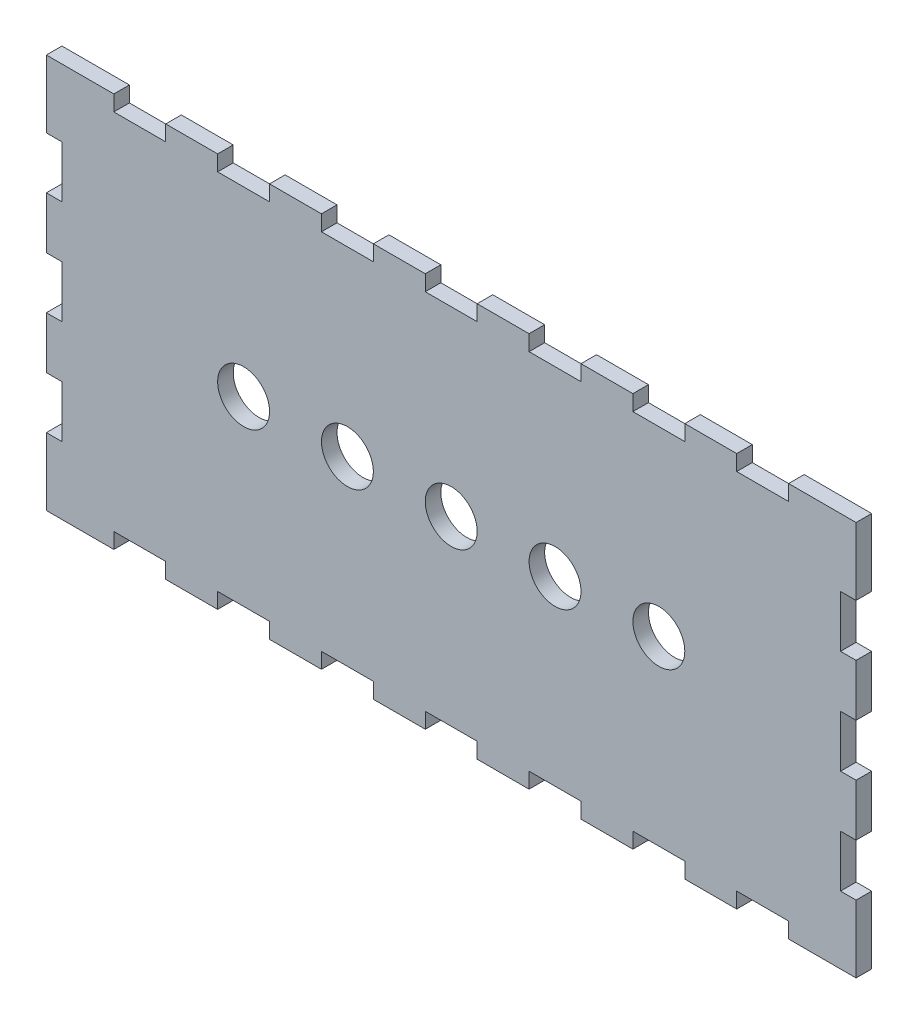
SolidWorks part; units mm, degrees
ref_plane "Front Plane" through (0, 0, 0) normal (0, 0, 1) x (1, 0, 0)
ref_plane "Top Plane" through (0, 0, 0) normal (0, 1, 0) x (1, 0, 0)
ref_plane "Right Plane" through (0, 0, 0) normal (1, 0, 0) x (0, 0, -1)
sketch "Sketch1" plane through (0, 0, 0) normal (0, 0, 1) x (1, 0, 0)
  line L0 (0, 73) -> (0, -3) construction
  line L1 (0, 35) -> (150, 35) construction
  line L2 (0, 60) -> (0, 50)
  line L3 (75, 35) -> (75, 12.9355) construction
  line L4 (153, 73) -> (150, 73)
  line L5 (-3, 70) -> (-3, 60)
  line L6 (-3, 60) -> (0, 60)
  line L7 (0, 50) -> (-3, 50)
  line L8 (-3, 50) -> (-3, 40)
  line L9 (0, 40) -> (0, 30)
  line L10 (-3, 40) -> (0, 40)
  line L11 (0, 30) -> (-3, 30)
  line L12 (-3, 30) -> (-3, 20)
  line L13 (0, 20) -> (0, 10)
  line L14 (-3, 20) -> (0, 20)
  line L15 (0, 10) -> (-3, 10)
  line L16 (-3, 10) -> (-3, 0)
  line L17 (75, 35) -> (35, 35)
  line L18 (-3, 0) -> (0, 0)
  line L19 (0, 0) -> (0, -10) [skipped]
  line L20 (150, 20) -> (150, 10)
  line L21 (150, 40) -> (150, 30)
  line L22 (150, 60) -> (150, 50)
  line L24 (150, 10) -> (153, 10)
  line L25 (153, 20) -> (150, 20)
  line L26 (150, 30) -> (153, 30)
  line L27 (153, 40) -> (150, 40)
  line L28 (150, 50) -> (153, 50)
  line L29 (130, 73) -> (130, 70)
  line L30 (153, 60) -> (150, 60)
  line L31 (153, 10) -> (153, 0)
  line L32 (153, 30) -> (153, 20)
  line L33 (153, 50) -> (153, 40)
  line L34 (153, 70) -> (153, 60)
  line L35 (150, 73) -> (140, 73)
  line L36 (153, 70) -> (153, 73)
  line L37 (140, 73) -> (140, 70)
  line L38 (140, 70) -> (130, 70)
  line L39 (130, 73) -> (120, 73)
  line L40 (120, 70) -> (110, 70)
  line L41 (120, 73) -> (120, 70)
  line L42 (110, 73) -> (110, 70)
  line L43 (110, 73) -> (100, 73)
  line L44 (100, 70) -> (90, 70)
  line L45 (100, 73) -> (100, 70)
  line L46 (90, 73) -> (90, 70)
  line L47 (90, 73) -> (80, 73)
  line L48 (80, 70) -> (70, 70)
  line L49 (80, 73) -> (80, 70)
  line L50 (70, 73) -> (70, 70)
  line L51 (70, 73) -> (60, 73)
  line L52 (60, 70) -> (50, 70)
  line L53 (60, 73) -> (60, 70)
  line L54 (50, 73) -> (50, 70)
  line L55 (50, 73) -> (40, 73)
  line L56 (40, 70) -> (30, 70)
  line L57 (40, 73) -> (40, 70)
  line L58 (30, 73) -> (30, 70)
  line L59 (30, 73) -> (20, 73)
  line L60 (20, 70) -> (10, 70)
  line L61 (20, 73) -> (20, 70)
  line L62 (10, 70) -> (10, 73)
  line L63 (10, 73) -> (0, 73)
  line L64 (-3, -3) -> (-3, 0)
  line L65 (0, 73) -> (-3, 73)
  line L66 (-3, 73) -> (-3, 70)
  line L67 (0, -3) -> (-3, -3)
  line L68 (10, -3) -> (0, -3)
  line L69 (10, 0) -> (10, -3)
  line L70 (20, -3) -> (20, 0)
  line L71 (20, 0) -> (10, 0)
  line L72 (30, -3) -> (20, -3)
  line L73 (30, -3) -> (30, 0)
  line L74 (40, -3) -> (40, 0)
  line L75 (40, 0) -> (30, 0)
  line L76 (50, -3) -> (40, -3)
  line L77 (50, -3) -> (50, 0)
  line L78 (60, -3) -> (60, 0)
  line L79 (60, 0) -> (50, 0)
  line L80 (70, -3) -> (60, -3)
  line L81 (70, -3) -> (70, 0)
  line L82 (80, -3) -> (80, 0)
  line L83 (80, 0) -> (70, 0)
  line L84 (90, -3) -> (80, -3)
  line L85 (90, -3) -> (90, 0)
  line L86 (100, -3) -> (100, 0)
  line L87 (100, 0) -> (90, 0)
  line L88 (110, -3) -> (100, -3)
  line L89 (110, -3) -> (110, 0)
  line L90 (120, -3) -> (120, 0)
  line L91 (120, 0) -> (110, 0)
  line L92 (130, -3) -> (120, -3)
  line L93 (140, 0) -> (130, 0)
  line L94 (140, -3) -> (140, 0)
  line L95 (153, 0) -> (153, -3)
  line L96 (150, -3) -> (140, -3)
  line L97 (130, -3) -> (130, 0)
  line L98 (153, -3) -> (150, -3)
  circle A0 centre (35, 35) radius 5
  circle A1 centre (55, 35) radius 5
  circle A2 centre (75, 35) radius 5
  circle A3 centre (95, 35) radius 5
  circle A4 centre (115, 35) radius 5
  dimension "D1" = 4
  dimension "D2" = 7
extrude "Boss-Extrude1" add sketch "Sketch1" along normal blind 3 contours L98 L95 L31 L24 L20 L25 L32 L26 L21 L27 L33 L28 L22 L30 L34 L36 L4 L35 L37 L38 L29 L39 L41 L40 L42 L43 L45 L44 L46 L47 L49 L48 L50 L51 L53 L52 L54 L55 L57 L56 L58 L59 L61 L60 L62 L63 L65 L66 L5 L6 L2
